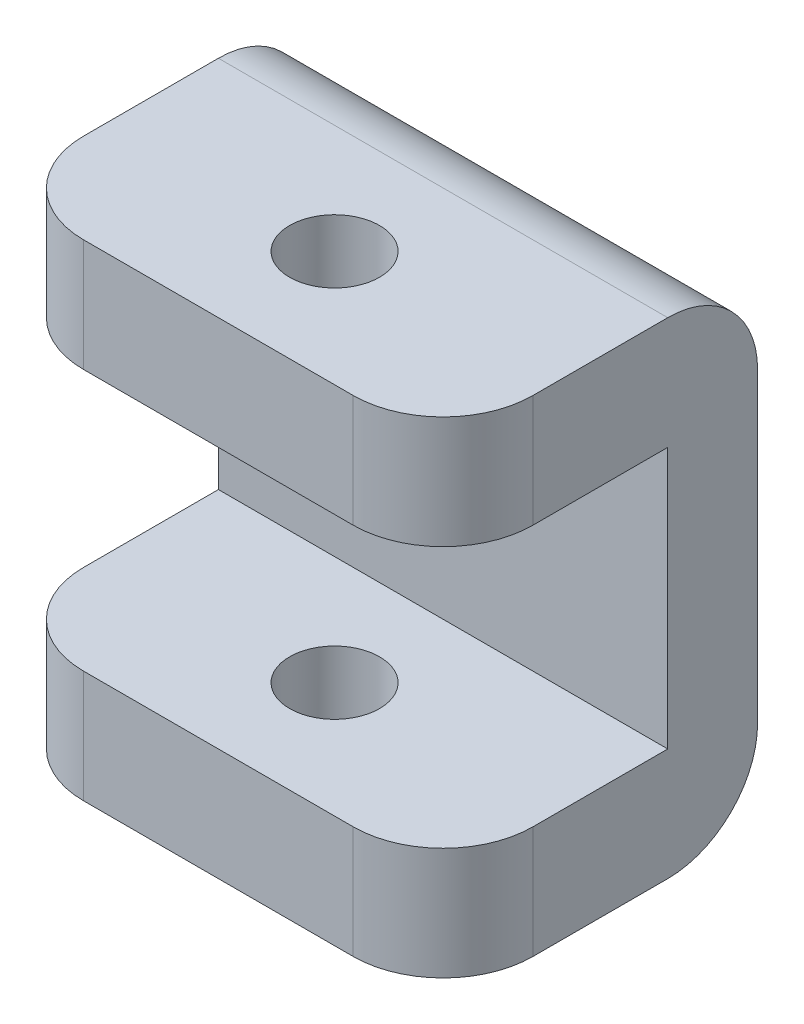
SolidWorks part; units mm, degrees
ref_plane "Front Plane" through (0, 0, 0) normal (0, 0, 1) x (1, 0, 0)
ref_plane "Top Plane" through (0, 0, 0) normal (0, 1, 0) x (1, 0, 0)
ref_plane "Right Plane" through (0, 0, 0) normal (1, 0, 0) x (0, 0, -1)
sketch "Sketch1" plane through (0, 0, 0) normal (0, 0, 1) x (1, 0, 0)
  line L1 (-8.3333, 3.9312) -> (1.6667, 3.9312)
  line L2 (-8.3333, 3.9312) -> (-8.3333, -6.8818)
  line L3 (-8.3333, -6.8818) -> (1.6667, -6.8818)
  line L4 (1.6667, 3.9312) -> (1.6667, -6.8818)
  dimension "D1" = 10
  dimension "D2" = 10.813
extrude "Boss-Extrude1" add sketch "Sketch1" along normal blind 2
sketch "Sketch2" plane through (0, 0, 2) normal (0, 0, 1) x (1, 0, 0)
  line L0 (1.6667, -6.8818) -> (1.6667, 3.9312) construction
  line L1 (-8.3333, 3.9312) -> (1.6667, 3.9312)
  line L2 (-8.3333, 3.9312) -> (-8.3333, 1.4312)
  line L3 (-8.3333, 1.4312) -> (1.6667, 1.4312)
  line L4 (1.6667, 3.9312) -> (1.6667, 1.4312)
  line L5 (-8.3333, 3.9312) -> (-8.3333, -6.8818) construction
  line L6 (1.6667, -6.8818) -> (-8.3333, -6.8818)
  line L7 (1.6667, -6.8818) -> (1.6667, -4.3818)
  line L8 (1.6667, -4.3818) -> (-8.3333, -4.3818)
  line L9 (-8.3333, -6.8818) -> (-8.3333, -4.3818)
  dimension "D1" = 2.5
  dimension "D2" = 2.5
extrude "Boss-Extrude2" add sketch "Sketch2" along normal blind 5
sketch "Sketch3" plane through (0, 3.9312, 0) normal (0, 1, 0) x (1, 0, 0)
  line L0 (1.6667, -7) -> (-8.3333, -7) construction
  line L1 (-8.3333, -7) -> (-8.3333, 0) construction
  circle A0 centre (-3.3186, -4.43) radius 1
  dimension "D1" = 2
  dimension "D2" = 2.57
  dimension "D3" = 5.0147
extrude "Cut-Extrude1" cut sketch "Sketch3" against normal through all contours A0
fillet "Fillet2" radius 2 6 edges at (-3.3333, -6.8818, 0) (-3.3333, 3.9312, 0) (-8.3333, -5.6318, 7) (1.6667, -5.6318, 7) (1.6667, 2.6812, 7) (-8.3333, 2.6812, 7)
